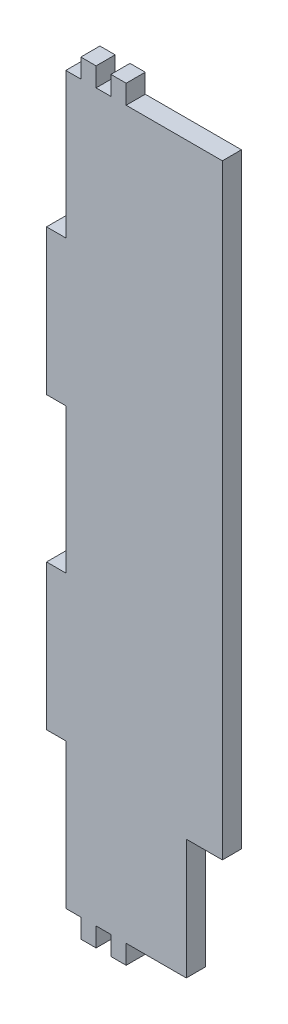
SolidWorks part; units mm, degrees
ref_plane "Front Plane" through (0, 0, 0) normal (0, 0, 1) x (1, 0, 0)
ref_plane "Top Plane" through (0, 0, 0) normal (0, 1, 0) x (1, 0, 0)
ref_plane "Right Plane" through (0, 0, 0) normal (1, 0, 0) x (0, 0, -1)
sketch "Sketch1" plane through (0, 0, 0) normal (0, 0, 1) x (1, 0, 0)
  line L0 (-12.5, 0) -> (12.5, 0) construction
  line L1 (12.5, 120.6625) -> (-12.5, 120.6625)
  line L2 (12.5, 120.6625) -> (12.5, -120.6625)
  line L3 (12.5, -120.6625) -> (-12.5, -120.6625)
  line L4 (-12.5, 120.6625) -> (-12.5, -120.6625)
  line L5 (12.5, 120.6625) -> (-12.5, -120.6625) construction
  line L6 (12.5, -120.6625) -> (-12.5, 120.6625) construction
  line L7 (-7.5, 120.6625) -> (-2.5, 120.6625)
  line L8 (-7.5, 120.6625) -> (-7.5, 127.0125)
  line L9 (-7.5, 127.0125) -> (-2.5, 127.0125)
  line L10 (-2.5, 120.6625) -> (-2.5, 127.0125)
  line L11 (2.5, 120.6625) -> (7.5, 120.6625)
  line L12 (2.5, 120.6625) -> (2.5, 127.0125)
  line L13 (2.5, 127.0125) -> (7.5, 127.0125)
  line L14 (7.5, 120.6625) -> (7.5, 127.0125)
  line L15 (7.5, -120.6625) -> (7.5, -127.0125)
  line L16 (-12.5, 72.3975) -> (-18.9, 72.3975)
  line L17 (-12.5, 72.3975) -> (-12.5, 24.1325)
  line L18 (-12.5, 24.1325) -> (-18.9, 24.1325)
  line L19 (-18.9, 72.3975) -> (-18.9, 24.1325)
  line L20 (-12.5, -24.1325) -> (-18.9, -24.1325)
  line L21 (-12.5, -24.1325) -> (-12.5, -72.3975)
  line L22 (-12.5, -72.3975) -> (-18.9, -72.3975)
  line L23 (-18.9, -24.1325) -> (-18.9, -72.3975)
  line L24 (2.5, -127.0125) -> (7.5, -127.0125)
  line L25 (2.5, -120.6625) -> (2.5, -127.0125)
  line L26 (-2.5, -120.6625) -> (-2.5, -127.0125)
  line L27 (-7.5, -127.0125) -> (-2.5, -127.0125)
  line L28 (-7.5, -120.6625) -> (-7.5, -127.0125)
  line L30 (12.5, 120.6625) -> (27.5, 120.6625)
  line L31 (12.5, 120.6625) -> (12.5, -120.6625)
  line L32 (12.5, -120.6625) -> (27.5, -120.6625)
  line L33 (27.5, 120.6625) -> (27.5, -120.6625)
  line L34 (27.5, 120.6625) -> (39.5, 120.6625)
  line L35 (27.5, 120.6625) -> (27.5, -80.6625)
  line L36 (27.5, -80.6625) -> (39.5, -80.6625)
  line L37 (39.5, 120.6625) -> (39.5, -80.6625)
  point P0 (0, 0)
  dimension "D1" = 241.325
  dimension "D2" = 25
  dimension "D3" = 5
  dimension "D4" = 5
  dimension "D5" = 5
  dimension "D6" = 5
  dimension "D7" = 6.35
  dimension "D8" = 6.35
  dimension "D9" = 6.4
  dimension "D10" = 48.265
  dimension "D11" = 48.265
  dimension "D12" = 6.4
  dimension "D13" = 48.265
  dimension "D14" = 48.265
  dimension "D15" = 15
  dimension "D16" = 12
  dimension "D17" = 40
extrude "Boss-Extrude1" add sketch "Sketch1" along normal blind 6.35 contours L1 L10 L9 L8 | L1 L14 L13 L12 | L1 L4 L3 L2 | L16 L19 L18 L4 | L20 L23 L22 L4 | L3 L28 L27 L26 | L3 L25 L24 L15 | L33 L30 L2 L32 | L37 L34 L33 L36
sketch "Sketch2" plane through (0, 0, 6.35) normal (0, 0, 1) x (1, 0, 0)
  line L30 (27.5406, -120.7031) -> (27.5406, -80.7031)
  line L31 (27.5406, -120.7031) -> (27.5406, -80.7031)
  line L32 (27.5406, -80.7031) -> (39.5406, -80.7031)
  line L33 (27.5406, -80.7031) -> (39.5406, -80.7031)
  line L34 (39.5406, -80.7031) -> (39.5406, 120.7031)
  line L35 (39.5406, -80.7031) -> (39.5406, 120.7031)
  line L56 (-7.5406, 127.0531) -> (-7.5406, 120.7031)
  line L57 (-7.5406, 120.7031) -> (-12.5406, 120.7031)
  line L58 (-12.5406, 120.7031) -> (-12.5406, 72.4381)
  line L59 (-12.5406, 72.4381) -> (-18.9406, 72.4381)
  line L60 (-18.9406, 72.4381) -> (-18.9406, 24.0919)
  line L61 (-18.9406, 24.0919) -> (-12.5406, 24.0919)
  line L62 (-12.5406, 24.0919) -> (-12.5406, -24.0919)
  line L63 (-12.5406, -24.0919) -> (-18.9406, -24.0919)
  line L64 (-18.9406, -24.0919) -> (-18.9406, -72.4381)
  line L65 (-18.9406, -72.4381) -> (-12.5406, -72.4381)
  line L66 (-12.5406, -72.4381) -> (-12.5406, -120.7031)
  line L67 (-12.5406, -120.7031) -> (-7.5406, -120.7031)
  line L68 (-7.5406, -120.7031) -> (-7.5406, -127.0531)
  line L69 (-7.5406, -127.0531) -> (-2.4594, -127.0531)
  line L70 (-2.4594, -127.0531) -> (-2.4594, -120.7031)
  line L71 (-2.4594, -120.7031) -> (2.4594, -120.7031)
  line L72 (2.4594, -120.7031) -> (2.4594, -127.0531)
  line L73 (2.4594, -127.0531) -> (7.5406, -127.0531)
  line L74 (7.5406, -127.0531) -> (7.5406, -120.7031)
  line L75 (7.5406, -120.7031) -> (27.5406, -120.7031)
  line L77 (39.5406, 120.7031) -> (7.5406, 120.7031)
  line L78 (7.5406, 120.7031) -> (7.5406, 127.0531)
  line L79 (7.5406, 127.0531) -> (2.4594, 127.0531)
  line L80 (2.4594, 127.0531) -> (2.4594, 120.7031)
  line L81 (2.4594, 120.7031) -> (-2.4594, 120.7031)
  line L82 (-2.4594, 120.7031) -> (-2.4594, 127.0531)
  line L83 (-2.4594, 127.0531) -> (-7.5406, 127.0531)
  line L84 (-7.5406, 127.0531) -> (-7.5406, 120.7031)
  line L85 (-7.5406, 120.7031) -> (-12.5406, 120.7031)
  line L86 (-12.5406, 120.7031) -> (-12.5406, 72.4381)
  line L87 (-12.5406, 72.4381) -> (-18.9406, 72.4381)
  line L88 (-18.9406, 72.4381) -> (-18.9406, 24.0919)
  line L89 (-18.9406, 24.0919) -> (-12.5406, 24.0919)
  line L90 (-12.5406, 24.0919) -> (-12.5406, -24.0919)
  line L91 (-12.5406, -24.0919) -> (-18.9406, -24.0919)
  line L92 (-18.9406, -24.0919) -> (-18.9406, -72.4381)
  line L93 (-18.9406, -72.4381) -> (-12.5406, -72.4381)
  line L94 (-12.5406, -72.4381) -> (-12.5406, -120.7031)
  line L95 (-12.5406, -120.7031) -> (-7.5406, -120.7031)
  line L96 (-7.5406, -120.7031) -> (-7.5406, -127.0531)
  line L97 (-7.5406, -127.0531) -> (-2.4594, -127.0531)
  line L98 (-2.4594, -127.0531) -> (-2.4594, -120.7031)
  line L99 (-2.4594, -120.7031) -> (2.4594, -120.7031)
  line L100 (2.4594, -120.7031) -> (2.4594, -127.0531)
  line L101 (2.4594, -127.0531) -> (7.5406, -127.0531)
  line L102 (7.5406, -127.0531) -> (7.5406, -120.7031)
  line L103 (7.5406, -120.7031) -> (27.5406, -120.7031)
  line L105 (39.5406, 120.7031) -> (7.5406, 120.7031)
  line L106 (7.5406, 120.7031) -> (7.5406, 127.0531)
  line L107 (7.5406, 127.0531) -> (2.4594, 127.0531)
  line L108 (2.4594, 127.0531) -> (2.4594, 120.7031)
  line L109 (2.4594, 120.7031) -> (-2.4594, 120.7031)
  line L110 (-2.4594, 120.7031) -> (-2.4594, 127.0531)
  line L111 (-2.4594, 127.0531) -> (-7.5406, 127.0531)
  dimension "D1" = 0.0406
extrude "Boss-Extrude2" add sketch "Sketch2" against normal up to surface (6.35 mm away) up to face at (-0.5533, -5.3775, 0)
